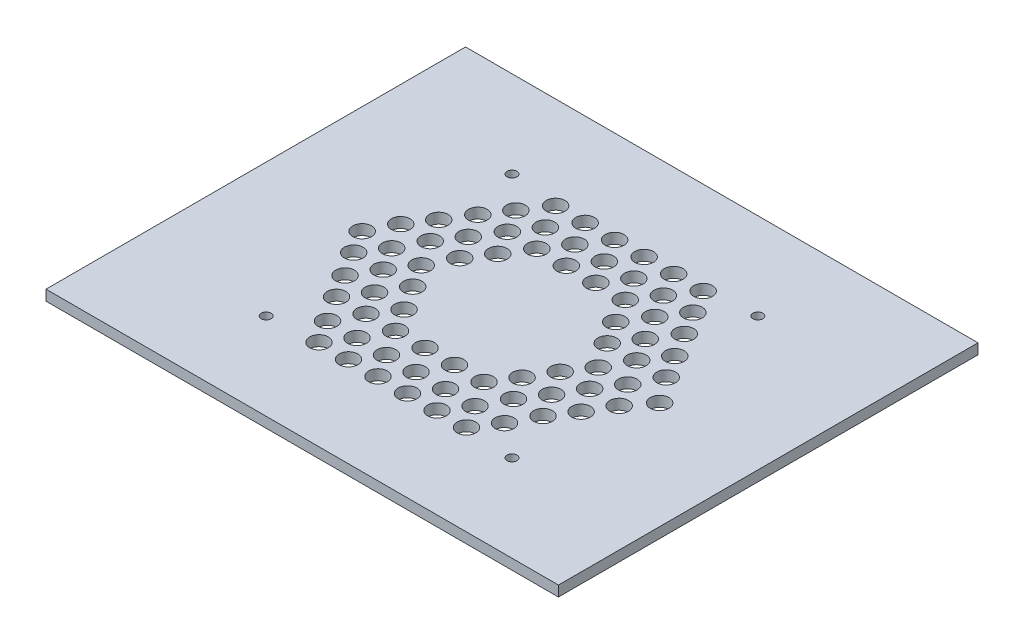
SolidWorks part; units mm, degrees
ref_plane "Front Plane" through (0, 0, 0) normal (0, 0, 1) x (1, 0, 0)
ref_plane "Top Plane" through (0, 0, 0) normal (0, 1, 0) x (1, 0, 0)
ref_plane "Right Plane" through (0, 0, 0) normal (1, 0, 0) x (0, 0, -1)
sketch "Sketch1" plane through (0, 0, 0) normal (0, 1, 0) x (1, 0, 0)
  line L1 (-61.8618, 43.259) -> (94.4882, 43.259)
  line L2 (-61.8618, 43.259) -> (-61.8618, -84.741)
  line L3 (-61.8618, -84.741) -> (94.4882, -84.741)
  line L4 (94.4882, 43.259) -> (94.4882, -84.741)
  dimension "D1" = 156.35
  dimension "D2" = 128
extrude "Boss-Extrude1" add sketch "Sketch1" along normal blind 3.175
sketch "Sketch2" plane through (0, 0, 0) normal (0, -1, 0) x (1, 0, 0)
  line L0 (94.4882, 84.741) -> (94.4882, -43.259) construction
  line L1 (-23.6868, 60.741) -> (56.3132, 60.741)
  line L2 (-23.6868, 60.741) -> (-23.6868, -19.259)
  line L3 (-23.6868, -19.259) -> (56.3132, -19.259)
  line L4 (56.3132, 60.741) -> (56.3132, -19.259)
  line L5 (94.4882, -43.259) -> (-61.8618, -43.259) construction
  line L6 (-34.2801, 20.741) -> (61.361, 20.741)
  circle A0 centre (-21.1868, 58.241) radius 1.5
  circle A1 centre (53.8132, 58.241) radius 1.5
  circle A2 centre (53.8132, -16.759) radius 1.5
  circle A3 centre (-21.1868, -16.759) radius 1.5
  dimension "D5" = 2.5
  dimension "D6" = 2.5
  dimension "D7" = 2.5
  dimension "D8" = 2.5
  dimension "D9" = 3
  dimension "D10" = 3
  dimension "D1" = 80
  dimension "D2" = 80
  dimension "D3" = 38.175
  dimension "D4" = 24
  dimension "D11" = 40
extrude "Cut-Extrude1" cut sketch "Sketch2" against normal blind 10 contours A0 | A1 | A2 | A3
sketch "Sketch3" plane through (0, 0, 0) normal (0, -1, 0) x (1, 0, 0)
  circle A2 centre (-6.178, 57.136) radius 2.8575
  circle A3 centre (2.822, 57.136) radius 2.8575
  circle A4 centre (11.822, 57.136) radius 2.8575
  circle A5 centre (20.822, 57.136) radius 2.8575
  circle A6 centre (29.822, 57.136) radius 2.8575
  circle A7 centre (38.822, 57.136) radius 2.8575
  circle A12 centre (-10.5135, 50.1955) radius 2.8575
  circle A13 centre (-1.5135, 50.1955) radius 2.8575
  circle A14 centre (7.4865, 50.1955) radius 2.8575
  circle A15 centre (16.4865, 50.1955) radius 2.8575
  circle A16 centre (25.4865, 50.1955) radius 2.8575
  circle A17 centre (34.4865, 50.1955) radius 2.8575
  circle A18 centre (43.4865, 50.1955) radius 2.8575
  circle A21 centre (-15.5266, 42.4397) radius 2.8575
  circle A22 centre (-6.5266, 42.4397) radius 2.8575
  circle A23 centre (2.4734, 42.4397) radius 2.8575
  circle A24 centre (11.4734, 42.4397) radius 2.8575
  circle A25 centre (20.4734, 42.4397) radius 2.8575
  circle A26 centre (29.4734, 42.4397) radius 2.8575
  circle A27 centre (38.4734, 42.4397) radius 2.8575
  circle A28 centre (47.4734, 42.4397) radius 2.8575
  circle A31 centre (-19.8621, 35.4992) radius 2.8575
  circle A32 centre (-10.8621, 35.4992) radius 2.8575
  circle A33 centre (-1.8621, 35.4992) radius 2.8575
  circle A37 centre (34.1379, 35.4992) radius 2.8575
  circle A38 centre (43.1379, 35.4992) radius 2.8575
  circle A39 centre (52.1379, 35.4992) radius 2.8575
  circle A40 centre (-24.5941, 28.1376) radius 2.8575
  circle A41 centre (-15.5941, 28.1376) radius 2.8575
  circle A42 centre (-6.5941, 28.1376) radius 2.8575
  circle A47 centre (38.4059, 28.1376) radius 2.8575
  circle A48 centre (47.4059, 28.1376) radius 2.8575
  circle A49 centre (56.4059, 28.1376) radius 2.8575
  circle A50 centre (-28.9296, 21.1971) radius 2.8575
  circle A51 centre (-19.9296, 21.1971) radius 2.8575
  circle A52 centre (-10.9296, 21.1971) radius 2.8575
  circle A58 centre (43.0704, 21.1971) radius 2.8575
  circle A59 centre (52.0704, 21.1971) radius 2.8575
  circle A60 centre (-24.9427, 13.4412) radius 2.8575
  circle A61 centre (-15.9427, 13.4412) radius 2.8575
  circle A62 centre (-6.9427, 13.4412) radius 2.8575
  circle A67 centre (38.0573, 13.4412) radius 2.8575
  circle A68 centre (47.0573, 13.4412) radius 2.8575
  circle A69 centre (56.0573, 13.4412) radius 2.8575
  circle A71 centre (-20.2782, 6.5007) radius 2.8575
  circle A72 centre (-11.2782, 6.5007) radius 2.8575
  circle A73 centre (-2.2782, 6.5007) radius 2.8575
  circle A77 centre (33.7218, 6.5007) radius 2.8575
  circle A78 centre (42.7218, 6.5007) radius 2.8575
  circle A79 centre (51.7218, 6.5007) radius 2.8575
  circle A81 centre (-15.6622, -0.8055) radius 2.8575
  circle A82 centre (-6.6622, -0.8055) radius 2.8575
  circle A83 centre (2.3378, -0.8055) radius 2.8575
  circle A84 centre (11.3378, -0.8055) radius 2.8575
  circle A85 centre (20.3378, -0.8055) radius 2.8575
  circle A86 centre (29.3378, -0.8055) radius 2.8575
  circle A87 centre (38.3378, -0.8055) radius 2.8575
  circle A88 centre (47.3378, -0.8055) radius 2.8575
  circle A92 centre (-10.9977, -7.746) radius 2.8575
  circle A93 centre (-1.9977, -7.746) radius 2.8575
  circle A94 centre (7.0023, -7.746) radius 2.8575
  circle A95 centre (16.0023, -7.746) radius 2.8575
  circle A96 centre (25.0023, -7.746) radius 2.8575
  circle A97 centre (34.0023, -7.746) radius 2.8575
  circle A98 centre (43.0023, -7.746) radius 2.8575
  circle A161 centre (-6.1375, -15.019) radius 2.8575
  circle A162 centre (2.8625, -15.019) radius 2.8575
  circle A163 centre (11.8625, -15.019) radius 2.8575
  circle A164 centre (20.8625, -15.019) radius 2.8575
  circle A165 centre (29.8625, -15.019) radius 2.8575
  circle A166 centre (38.8625, -15.019) radius 2.8575
  circle A170 centre (61.8115, 21.1971) radius 2.8575
extrude "Cut-Extrude2" cut sketch "Sketch3" against normal blind 10
